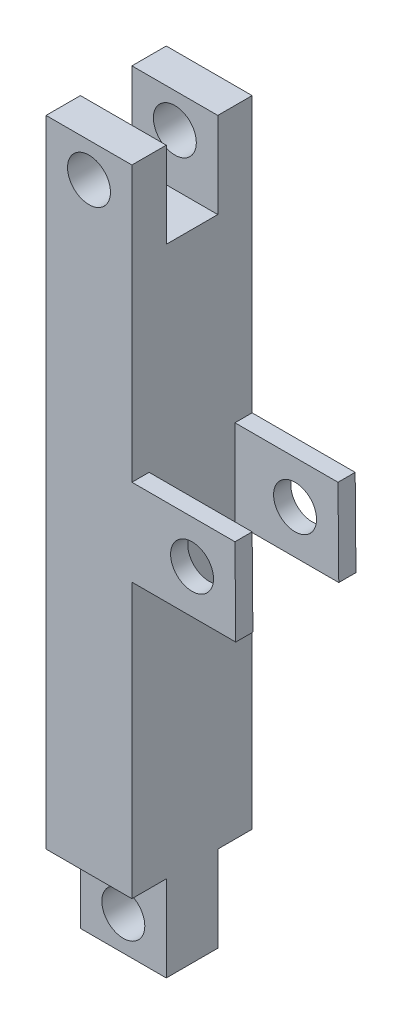
SolidWorks part; units mm, degrees
material "PEN"
ref_plane "前视基准面" through (0, 0, 0) normal (0, 0, 1) x (1, 0, 0)
ref_plane "上视基准面" through (0, 0, 0) normal (0, 1, 0) x (1, 0, 0)
ref_plane "右视基准面" through (0, 0, 0) normal (1, 0, 0) x (0, 0, -1)
sketch "草图1" plane through (0, 0, 0) normal (0, 1, 0) x (1, 0, 0)
  line L7 (5, 7) -> (-5, 7)
  line L8 (5, 7) -> (5, -7)
  line L9 (5, -7) -> (-5, -7)
  line L10 (-5, 7) -> (-5, -7)
  line L11 (5, 7) -> (-5, -7) construction
  line L12 (5, -7) -> (-5, 7) construction
  point P4 (2.5, 3.5)
extrude "凸台-拉伸1" add sketch "草图1" along normal mid plane 74
sketch "草图7" plane through (0, 0, 0) normal (0, 0, 1) x (1, 0, 0)
  line L0 (5, 37) -> (5, -37) construction
  line L1 (5, 5) -> (17, 5)
  line L9 (17.0903, -5.072) -> (5, -5.072)
  line L10 (5, -5.072) -> (5, 5)
  line L11 (17, 5) -> (17.0903, -5.072)
extrude "凸台-拉伸3" add sketch "草图7" along normal mid plane 14
sketch "草图8" plane through (0, 0, 0) normal (0, 0, 1) x (1, 0, 0)
  line L12 (5, 5) -> (17.0903, 5)
  line L13 (5, 5) -> (5, -5.072)
  line L14 (5, -5.072) -> (17.0903, -5.072)
  line L15 (17.0903, 5) -> (17.0903, -5.072)
  line L16 (5, 5) -> (17.0903, -5.072) construction
  line L17 (5, -5.072) -> (17.0903, 5) construction
  point P7 (11.0451, -0.036)
extrude "切除-拉伸3" cut sketch "草图8" against normal mid plane 10
sketch "草图10" plane through (0, 0, 0) normal (0, 0, 1) x (1, 0, 0)
  circle A2 centre (12, 0) radius 2.5
extrude "切除-拉伸4" cut sketch "草图10" against normal through all both and the other way through all
sketch "草图14" plane through (0, 0, 0) normal (0, 0, 1) x (1, 0, 0)
  line L0 (5, 37) -> (5, 5) construction
  line L1 (-5, 37) -> (5, 37)
  line L2 (-5, 37) -> (-5, 27)
  line L3 (-5, 27) -> (5, 27)
  line L4 (5, 37) -> (5, 27)
  line L5 (-5, 37) -> (5, 27) construction
  line L6 (-5, 27) -> (5, 37) construction
  point P5 (0, 32)
extrude "切除-拉伸8" cut sketch "草图14" against normal mid plane 6
sketch "草图15" plane through (0, 0, 0) normal (0, 0, 1) x (1, 0, 0)
  line L5 (-5, -37) -> (5, -37)
  line L6 (-5, -37) -> (-5, -47)
  line L7 (-5, -47) -> (5, -47)
  line L8 (5, -37) -> (5, -47)
  line L9 (-5, -37) -> (5, -47) construction
  line L10 (-5, -47) -> (5, -37) construction
  point P4 (0, -42)
extrude "凸台-拉伸4" add sketch "草图15" along normal mid plane 6
sketch "草图16" plane through (0, 0, 0) normal (0, 0, 1) x (1, 0, 0)
  circle A0 centre (0, 33) radius 2.5
extrude "切除-拉伸9" cut sketch "草图16" against normal through all both and the other way through all
sketch "草图17" plane through (0, 0, 0) normal (0, 0, 1) x (1, 0, 0)
  circle A0 centre (0, -43) radius 2.5
extrude "切除-拉伸10" cut sketch "草图17" against normal through all both and the other way through all
